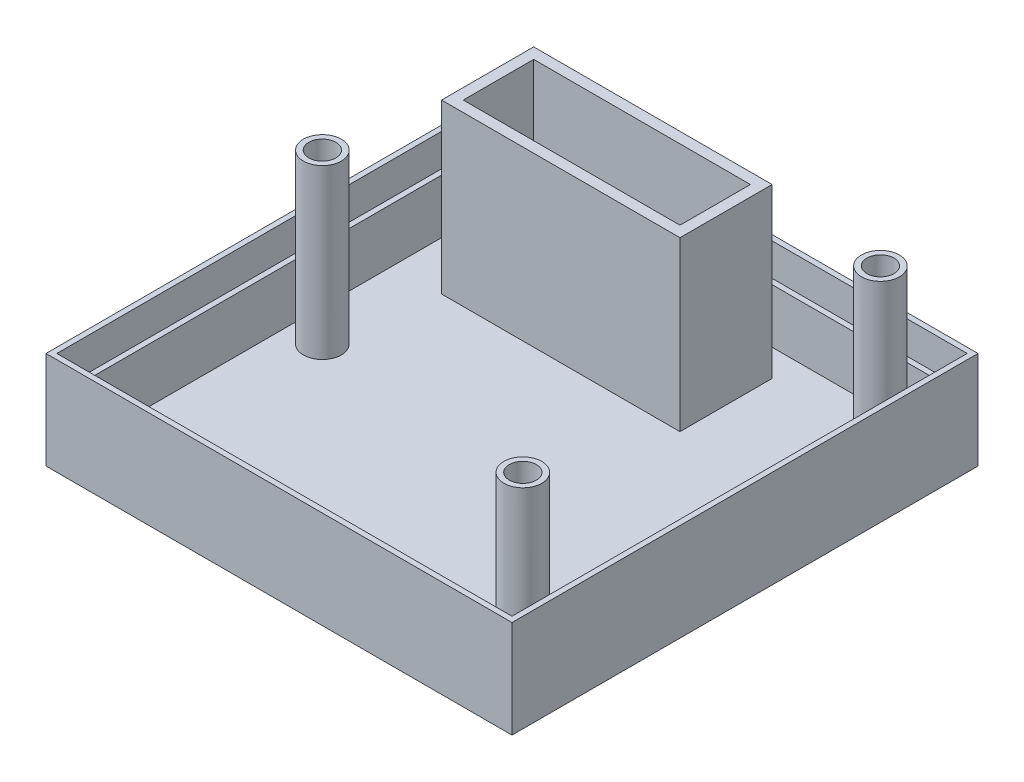
SolidWorks part; units mm, degrees
ref_plane "前视基准面" through (0, 0, 0) normal (0, 0, 1) x (1, 0, 0)
ref_plane "上视基准面" through (0, 0, 0) normal (0, 1, 0) x (1, 0, 0)
ref_plane "右视基准面" through (0, 0, 0) normal (1, 0, 0) x (0, 0, -1)
sketch "草图1" plane through (0, 0, 0) normal (0, 1, 0) x (1, 0, 0)
  line L1 (-21.5, -21.5) -> (21.5, -21.5)
  line L2 (-21.5, -21.5) -> (-21.5, 21.5)
  line L3 (-21.5, 21.5) -> (21.5, 21.5)
  line L4 (21.5, -21.5) -> (21.5, 21.5)
  line L5 (-21.5, -21.5) -> (21.5, 21.5) construction
  line L6 (-21.5, 21.5) -> (21.5, -21.5) construction
  point P0 (0, 0)
  dimension "D1" = 43
  dimension "D2" = 43
extrude "凸台-拉伸1" add sketch "草图1" along normal blind 9
sketch "草图2" plane through (0, 9, 0) normal (0, 1, 0) x (1, 0, 0)
  line L1 (-20.5, -20.5) -> (20.5, -20.5)
  line L2 (-20.5, -20.5) -> (-20.5, 20.5)
  line L3 (-20.5, 20.5) -> (20.5, 20.5)
  line L4 (20.5, -20.5) -> (20.5, 20.5)
  line L5 (-20.5, -20.5) -> (20.5, 20.5) construction
  line L6 (-20.5, 20.5) -> (20.5, -20.5) construction
  point P0 (0, 0)
  dimension "D1" = 41
  dimension "D2" = 41
extrude "切除-拉伸1" cut sketch "草图2" against normal blind 8
sketch "草图3" plane through (0, 1, 0) normal (0, 1, 0) x (1, 0, 0)
  line L0 (-20.5, 0) -> (20.5, 0) construction
  line L1 (-20.5, 20.5) -> (-20.5, -20.5) construction
  line L2 (20.5, -20.5) -> (20.5, 20.5) construction
  line L3 (17.5, 20.5) -> (17.5, 16.5) construction
  line L4 (20.5, 20.5) -> (-20.5, 20.5) construction
  line L5 (17.5, 16.5) -> (20.5, 16.5) construction
  line L6 (17.5, -20.5) -> (17.5, -16.5) construction
  line L7 (-20.5, -20.5) -> (20.5, -20.5) construction
  line L8 (17.5, -16.5) -> (20.5, -16.5) construction
  circle A0 centre (-17.5, 0) radius 1.75
  circle A3 centre (17.5, 16.5) radius 1.75
  circle A5 centre (17.5, -16.5) radius 1.75
  dimension "D1" = 3
  dimension "D2" = 3.5
  dimension "D9" = 3.5
  dimension "D11" = 3.5
  dimension "D4" = 4
  dimension "D5" = 3
  dimension "D6" = 4
  dimension "D7" = 3
extrude "凸台-拉伸2" add sketch "草图3" along normal blind 15.5
sketch "草图4" plane through (0, 9, 0) normal (0, 1, 0) x (1, 0, 0)
  line L1 (-21, -21) -> (21, -21)
  line L2 (-21, -21) -> (-21, 21)
  line L3 (-21, 21) -> (21, 21)
  line L4 (21, -21) -> (21, 21)
  line L5 (-21, -21) -> (21, 21) construction
  line L6 (-21, 21) -> (21, -21) construction
  line L7 (20.5, -20.5) -> (-20.5, -20.5)
  line L8 (20.5, -20.5) -> (20.5, 20.5)
  line L9 (20.5, 20.5) -> (-20.5, 20.5)
  line L10 (-20.5, -20.5) -> (-20.5, 20.5)
  line L11 (20.5, -20.5) -> (-20.5, 20.5) construction
  line L12 (20.5, 20.5) -> (-20.5, -20.5) construction
  point P0 (0, 0)
  point P6 (0, 0)
  dimension "D1" = 42
  dimension "D2" = 42
  dimension "D3" = 41
  dimension "D4" = 41
extrude "切除-拉伸2" cut sketch "草图4" against normal blind 3
sketch "草图7" plane through (0, 0, 0) normal (0, -1, 0) x (1, 0, 0)
  text T0 "Better++" font "黑体" height 4.5
extrude "切除-拉伸4" cut sketch "草图7" against normal blind 0.3
sketch "草图8" plane through (0, 0, 0) normal (0, -1, 0) x (1, 0, 0)
  text T0 "Voltage-Sensor" font "黑体" height 2
extrude "切除-拉伸5" cut sketch "草图8" against normal blind 0.3
sketch "草图11" plane through (0, 1, 0) normal (0, 1, 0) x (1, 0, 0)
  line L1 (-15, 17) -> (5, 17)
  line L2 (-15, 17) -> (-15, 10.5)
  line L3 (-15, 10.5) -> (5, 10.5)
  line L4 (5, 17) -> (5, 10.5)
  line L7 (-20.5, 20.5) -> (-20.5, -20.5) construction
  line L8 (20.5, 20.5) -> (-20.5, 20.5) construction
  dimension "D1" = 20
  dimension "D2" = 6.5
  dimension "D3" = 5.5
  dimension "D4" = 3.5
extrude "切除-拉伸7" cut sketch "草图11" against normal up to next
sketch "草图12" plane through (0, 1, 0) normal (0, 1, 0) x (1, 0, 0)
  line L0 (-15, 17) -> (-15, 10.5) construction
  line L1 (-16, 18) -> (6, 18)
  line L2 (-16, 18) -> (-16, 9.5)
  line L3 (-16, 9.5) -> (6, 9.5)
  line L4 (6, 18) -> (6, 9.5)
  line L5 (5, 17) -> (-15, 17) construction
  line L6 (5, 10.5) -> (5, 17) construction
  line L7 (-15, 10.5) -> (5, 10.5) construction
  line L9 (-15, 17) -> (5, 17)
  line L10 (-15, 17) -> (-15, 10.5)
  line L11 (-15, 10.5) -> (5, 10.5)
  line L12 (5, 17) -> (5, 10.5)
  dimension "D1" = 1
  dimension "D2" = 1
  dimension "D3" = 1
  dimension "D4" = 1
extrude "凸台-拉伸3" add sketch "草图12" along normal blind 15.5
hole_wizard "M3 螺纹孔1" positions "草图13" profile "草图14" tap size "M3" standard "GB"
sketch "草图13" plane through (0, 16.5, 0) normal (0, 1, 0) x (1, 0, 0)
  point P0 (-17.5, 0)
  point P3 (17.5, 16.5)
  point P6 (17.5, -16.5)
cosmetic thread "孔螺蚊线1" parameters "D2"=3
cosmetic thread "孔螺蚊线2" parameters "D2"=3
cosmetic thread "孔螺蚊线3" parameters "D2"=3
sketch "草图14" plane through (-17.5, 16.5, 0) normal (1, 0, 0) x (0, 0, 1)
  line L0 (0, 0) -> (0, 14.2511)
  line L1 (0, 14.2511) -> (1.25, 13.5)
  line L2 (1.25, 13.5) -> (1.25, 0)
  line L5 (1.25, 0) -> (0, 0)
  line L10 (0, 14.2511) -> (-1.25, 13.5) construction
  line L11 (0, -6.35) -> (0, 107.95) construction
  dimension "螺纹孔钻头直径" = 2.5
  dimension "螺纹孔钻头深度" = 13.5
  dimension "导头角度" = 118
